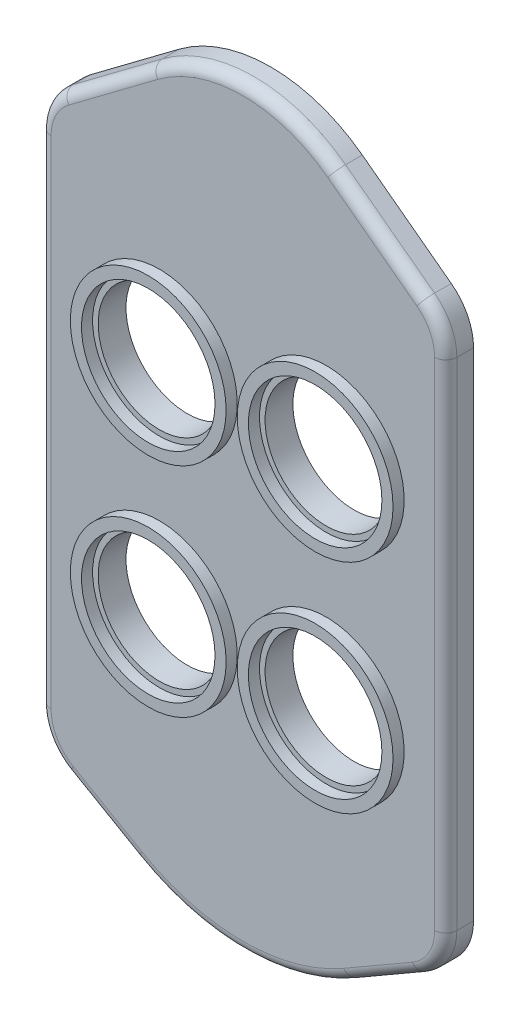
SolidWorks part; units mm, degrees
material "AISI 1020"
ref_plane "Front Plane" through (0, 0, 0) normal (0, 0, 1) x (1, 0, 0)
ref_plane "Top Plane" through (0, 0, 0) normal (0, 1, 0) x (1, 0, 0)
ref_plane "Right Plane" through (0, 0, 0) normal (1, 0, 0) x (0, 0, -1)
sketch "Sketch6" plane through (0, 0, 0) normal (0, 0, 1) x (1, 0, 0)
  line L0 (-32.4693, 53) -> (-16.4693, 65)
  line L2 (-36.4693, 45) -> (-36.4693, -44.2265)
  line L4 (36.4693, 45) -> (36.4693, -44.2265)
  line L5 (-36.4693, 50) -> (36.4693, -50) construction
  line L6 (-36.4693, -50) -> (36.4693, 50) construction
  line L7 (32.4693, 53) -> (16.4693, 65)
  line L8 (31.4693, -52.8868) -> (19.1488, -60)
  line L9 (-31.4693, -52.8868) -> (-19.1488, -60)
  arc A0 (-16.4693, 65) -> (16.4693, 65) centre (0, 43.0409) cw
  arc A1 (-19.1488, -60) -> (19.1488, -60) centre (0, -26.8332) ccw
  arc A2 (32.4693, 53) -> (36.4693, 45) centre (26.4693, 45) cw
  arc A3 (-32.4693, 53) -> (-36.4693, 45) centre (-26.4693, 45) ccw
  arc A4 (31.4693, -52.8868) -> (36.4693, -44.2265) centre (26.4693, -44.2265) ccw
  arc A5 (-36.4693, -44.2265) -> (-31.4693, -52.8868) centre (-26.4693, -44.2265) ccw
  point P0 (0, 0)
  dimension "D2" = 10
  dimension "D5" = 10
  dimension "D1" = 100
  dimension "D3" = 25
  dimension "D4" = 25
  dimension "D7" = 20
  dimension "D8" = 20
extrude "Boss-Extrude4" add sketch "Sketch6" along normal mid plane 5
sketch "Sketch7" plane through (0, 0, 2.5) normal (0, 0, 1) x (1, 0, 0)
  line L0 (0, 5.253) -> (0, -5.253) construction
  circle A1 centre (15, -19.1591) radius 11
  circle A2 centre (-15, -19.1591) radius 11
  circle A3 centre (-15, 20) radius 11
  circle A4 centre (15, 20) radius 11
  point P10 (0, 0)
  dimension "D1" = 22
  dimension "D2" = 22
  dimension "D3" = 22
  dimension "D5" = 22
  dimension "D6" = 30
  dimension "D4" = 30
  dimension "D7" = 20
extrude "Cut-Extrude1" cut sketch "Sketch7" against normal through all
sketch "Sketch8" plane through (0, 0, 2.5) normal (0, 0, 1) x (1, 0, 0)
  circle A0 centre (15, -19.1591) radius 12
  circle A1 centre (15, -19.1591) radius 14
  circle A2 centre (15, 20) radius 12
  circle A3 centre (-15, 20) radius 12
  circle A4 centre (-15, -19.1591) radius 12
  circle A5 centre (-15, 20) radius 14
  circle A6 centre (15, 20) radius 14
  circle A7 centre (-15, -19.1591) radius 14
  dimension "D1" = 24
  dimension "D3" = 24
  dimension "D4" = 24
  dimension "D5" = 24
  dimension "D2" = 2
  dimension "D6" = 2
extrude "Boss-Extrude5" add sketch "Sketch8" along normal blind 2
fillet "Fillet1" radius 2 12 edges at (35.1296, -49.2265, 2.5) (25.3091, -56.4434, 2.5) (0, -65.1309, 2.5) (-25.3091, -56.4434, 2.5) (-35.1296, -49.2265, 2.5) (-36.4693, 0.3868, 2.5) (-35.4136, 49.4721, 2.5) (-24.4693, 59, 2.5) (0, 70.4898, 2.5) (24.4693, 59, 2.5) (35.4136, 49.4721, 2.5) (36.4693, 0.3868, 2.5)
